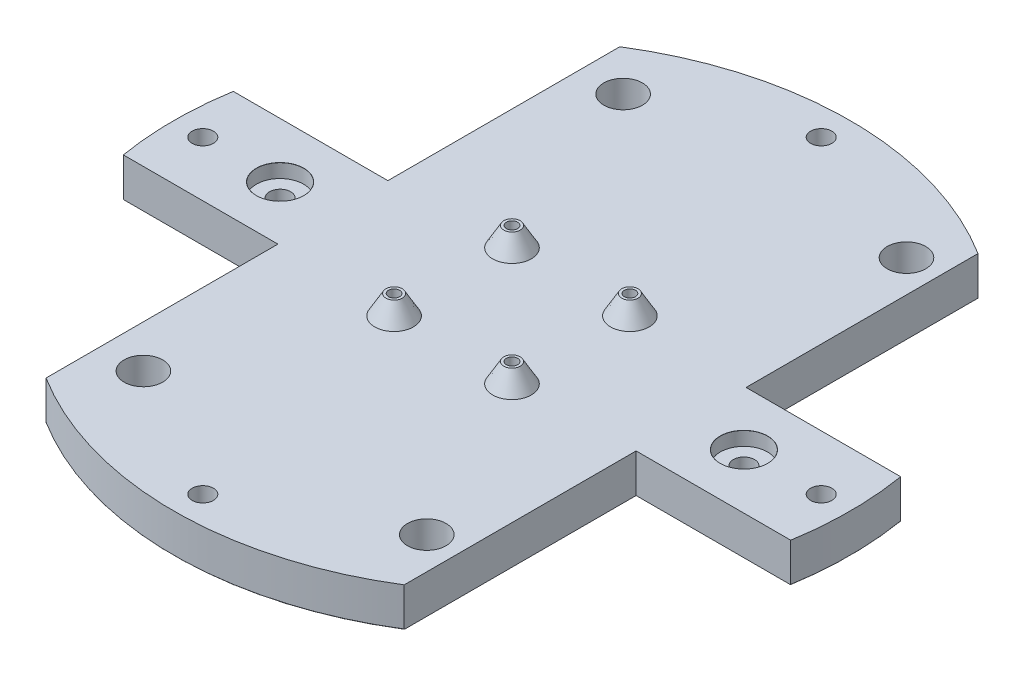
SolidWorks part; units mm, degrees
ref_plane "Front Plane" through (0, 0, 0) normal (0, 0, 1) x (1, 0, 0)
ref_plane "Top Plane" through (0, 0, 0) normal (0, 1, 0) x (1, 0, 0)
ref_plane "Right Plane" through (0, 0, 0) normal (1, 0, 0) x (0, 0, -1)
sketch "Sketch1" plane through (0, 0, 0) normal (0, 1, 0) x (1, 0, 0)
  circle A0 centre (0, 0) radius 87.5
  dimension "D1" = 175
extrude "Boss-Extrude1" add sketch "Sketch1" along normal blind 10
sketch "Sketch2" plane through (0, 10, 0) normal (0, 1, 0) x (1, 0, 0)
  circle A0 centre (0, -80) radius 7.5
  circle A1 centre (-80, 0) radius 7.5
  circle A2 centre (0, 80) radius 7.5
  circle A3 centre (80, 0) radius 7.5
  circle A4 centre (0, 0) radius 87.5 construction
  dimension "D1" = 15
extrude "Boss-Extrude2" add sketch "Sketch2" along normal blind 80
sketch "Sketch3" plane through (0, 0, 0) normal (0, -1, 0) x (-1, 0, 0)
  circle A0 centre (-80, 0) radius 7.5 construction
  circle A1 centre (0, 80) radius 7.5 construction
  circle A2 centre (80, 0) radius 7.5 construction
  circle A3 centre (0, -80) radius 7.5 construction
  point P0 (-80, 0)
  point P2 (0, 80)
  point P4 (80, 0)
  point P6 (0, -80)
hole_wizard "CBORE for M5 Hex Head Bolt1" positions "Sketch3" profile "Sketch4" counterbore size "M5" standard "ANSI Metric"
sketch "Sketch4" plane through (80, 0, 0) normal (1, 0, 0) x (0, 0, -1)
  line L0 (0, 0) -> (0, 21.6524)
  line L1 (0, 21.6524) -> (2.75, 20)
  line L2 (2.75, 20) -> (2.75, 3.58)
  line L3 (2.75, 3.58) -> (6.12, 3.58)
  line L5 (6.12, 3.58) -> (6.12, 0.025)
  line L6 (6.12, 0.025) -> (6.145, 0)
  line L7 (6.145, 0) -> (0, 0)
  line L8 (-6.12, 0.025) -> (-6.145, 0) construction
  line L10 (0, 21.6524) -> (-2.75, 20) construction
  line L11 (0, -6.35) -> (0, 107.95) construction
  dimension "Hole Dia." = 5.5
  dimension "Hole Depth" = 20
  dimension "C'Bore Dia." = 12.24
  dimension "C'Bore Depth" = 3.58
  dimension "Near C'Sink Dia." = 12.29
  dimension "Near C'Sink Angle" = 90
  dimension "Drill Angle" = 118
sketch "Sketch5" plane through (0, 10, 0) normal (0, 1, 0) x (1, 0, 0)
  circle A0 centre (0, 0) radius 87.5
  arc A1 (0, 87.5) -> (-87.5, 0) centre (0, 0) ccw construction
extrude "Cut-Extrude1" cut sketch "Sketch5" along normal blind 80
fillet "Fillet1" radius 0.1 1 edges at (0, 0, 87.5)
sketch "Sketch6" plane through (0, 10, 0) normal (0, 1, 0) x (1, 0, 0)
  line L5 (-15.25, 15.25) -> (15.25, 15.25) construction
  line L6 (-15.25, 15.25) -> (-15.25, -15.25) construction
  line L7 (-15.25, -15.25) -> (15.25, -15.25) construction
  line L8 (15.25, 15.25) -> (15.25, -15.25) construction
  line L9 (0, -15.25) -> (0, 15.25) construction
  line L10 (-15.25, 0) -> (15.25, 0) construction
  circle A2 centre (-15.25, 15.25) radius 5
  circle A3 centre (15.25, 15.25) radius 5
  circle A4 centre (15.25, -15.25) radius 5
  circle A5 centre (-15.25, -15.25) radius 5
  point P0 (0, 0)
  dimension "D3" = 10
  dimension "D1" = 30.5
  dimension "D2" = 30.5
extrude "Boss-Extrude3" add sketch "Sketch6" along normal blind 5 draft 30
sketch "Sketch7" plane through (0, 15, 0) normal (0, 1, 0) x (1, 0, 0)
  circle A0 centre (-15.25, 15.25) radius 1.45
  circle A1 centre (15.25, 15.25) radius 1.45
  circle A2 centre (15.25, -15.25) radius 1.45
  circle A3 centre (-15.25, -15.25) radius 1.45
  dimension "D1" = 2.9
extrude "Cut-Extrude2" cut sketch "Sketch7" against normal blind 8
sketch "Sketch9" plane through (0, 0, 0) normal (0, -1, 0) x (1, 0, 0)
  circle A0 centre (38.0033, 60.0533) radius 5
  arc A1 (32.7, 47.25) -> (25.2, 54.75) centre (32.7, 54.75) ccw construction
  circle A2 centre (-35.3033, 60.0533) radius 5
  arc A3 (-22.5, 54.75) -> (-30, 47.25) centre (-30, 54.75) ccw construction
  circle A4 centre (-35.3033, -64.0533) radius 5
  arc A5 (-30, -51.25) -> (-22.5, -58.75) centre (-30, -58.75) ccw construction
  circle A6 centre (38.0033, -64.0533) radius 5
  arc A7 (25.2, -58.75) -> (32.7, -51.25) centre (32.7, -58.75) ccw construction
  circle A8 centre (-30, -58.75) radius 5 construction
extrude "Cut-Extrude3" cut sketch "Sketch9" against normal blind 10
sketch "Sketch10" plane through (0, 0, 0) normal (0, -1, 0) x (1, 0, 0)
  line L4 (0, -8.25) -> (0, 8.25) construction
  line L9 (-86.3361, -14.2241) -> (-46.3361, -14.2241)
  line L10 (-46.3361, -14.2241) -> (-46.3361, -74.2241)
  line L11 (-46.3361, 14.2241) -> (-46.3361, 74.2241)
  line L12 (-46.3361, 14.2241) -> (-86.3361, 14.2241)
  line L13 (46.3361, 14.2241) -> (86.3361, 14.2241)
  line L14 (46.3361, 14.2241) -> (46.3361, 74.2241)
  line L15 (46.3361, -14.2241) -> (46.3361, -74.2241)
  line L16 (86.3361, -14.2241) -> (46.3361, -14.2241)
  arc A0 (46.3361, 74.2241) -> (86.3361, 14.2241) centre (0, 0) cw
  circle A5 centre (0, 0) radius 87.5 construction
  arc A6 (-86.3361, -14.2241) -> (-46.3361, -74.2241) centre (0, 0) ccw
  arc A7 (-46.3361, 74.2241) -> (-86.3361, 14.2241) centre (0, 0) ccw
  arc A8 (86.3361, -14.2241) -> (46.3361, -74.2241) centre (0, 0) cw
  dimension "D1" = 60
  dimension "D2" = 40
  dimension "D3" = 60
extrude "Cut-Extrude5" cut sketch "Sketch10" against normal blind 10
sketch "Sketch12" plane through (0, 10, 0) normal (0, 1, 0) x (1, 0, 0)
  circle A0 centre (-80, 0) radius 2.75 construction
  circle A1 centre (80, 0) radius 2.75 construction
  point P0 (-60, 0)
  point P2 (60, 0)
  dimension "D1" = 20
  dimension "D2" = 20
hole_wizard "CBORE for M5 Hex Head Bolt2" positions "Sketch12" profile "Sketch13" counterbore size "M5" standard "ANSI Metric" end condition through all
sketch "Sketch13" plane through (-60, 10, 0) normal (1, 0, 0) x (0, 0, 1)
  line L0 (0, 0) -> (0, 10)
  line L1 (0, 10) -> (2.75, 10)
  line L3 (2.75, 10) -> (2.75, 3.58)
  line L4 (6.12, 3.58) -> (2.75, 3.58)
  line L5 (6.12, 3.58) -> (6.12, 0.025)
  line L6 (6.12, 0.025) -> (6.145, 0)
  line L7 (6.145, 0) -> (0, 0)
  line L8 (-6.12, 0.025) -> (-6.145, 0) construction
  line L11 (0, -6.35) -> (0, 107.95) construction
  dimension "Thru Hole Dia." = 5.5
  dimension "Thru Hole Depth" = 10
  dimension "C'Bore Dia." = 12.24
  dimension "C'Bore Depth" = 3.58
  dimension "Near C'Sink Dia." = 12.29
  dimension "Near C'Sink Angle" = 90
